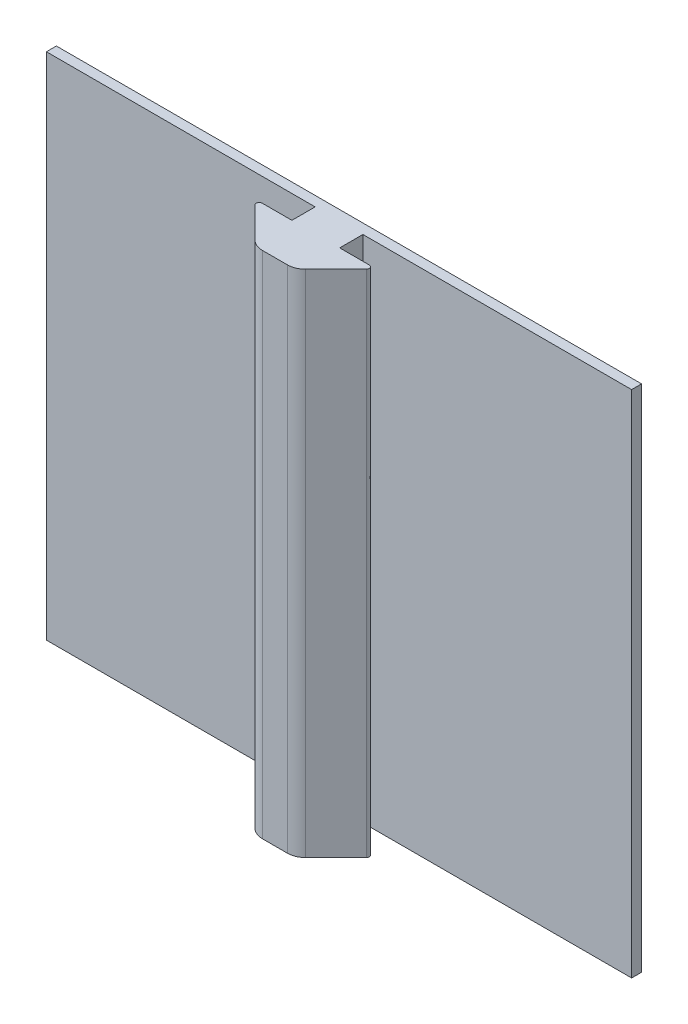
SolidWorks part; units mm, degrees
ref_plane "Front Plane" through (0, 0, 0) normal (0, 0, 1) x (1, 0, 0)
ref_plane "Top Plane" through (0, 0, 0) normal (0, 1, 0) x (1, 0, 0)
ref_plane "Right Plane" through (0, 0, 0) normal (1, 0, 0) x (0, 0, -1)
sketch "Sketch2" plane through (0, 273.2772, 0) normal (0, 1, 0) x (1, 0, 0)
  line L71 (-29.4517, 3.1399) -> (-29.4517, 3.3117)
  line L72 (-29.4517, 3.3117) -> (-63.7417, 3.3117)
  line L73 (-26.4037, -5.1151) -> (-26.4037, 8.1768) construction
  line L74 (-24.8068, -5.1151) -> (-28.0005, -5.1151) construction
  line L75 (-23.3557, 3.3117) -> (10.9343, 3.3117)
  line L76 (-23.3557, 3.1399) -> (-23.3557, 3.3117)
  line L77 (-63.7417, 3.3117) -> (-63.7417, 4.5817)
  line L78 (-29.4517, 0.3459) -> (-29.4517, 3.1399)
  line L79 (-33.2346, 0.3459) -> (-29.4517, 0.3459)
  line L80 (-29.6169, -4.1915) -> (-33.504, -0.3045)
  line L81 (-24.8068, -4.8611) -> (-28.0005, -4.8611)
  line L82 (-19.3033, -0.3045) -> (-23.1904, -4.1915)
  line L83 (-23.3557, 0.3459) -> (-19.5727, 0.3459)
  line L84 (-23.3557, 3.1399) -> (-23.3557, 0.3459)
  line L85 (-29.4517, 0.3459) -> (-29.4517, 3.1399)
  line L86 (-33.2346, 0.3459) -> (-29.4517, 0.3459)
  line L87 (-29.6169, -4.1915) -> (-33.504, -0.3045)
  line L88 (-24.8068, -4.8611) -> (-28.0005, -4.8611)
  line L89 (-19.3033, -0.3045) -> (-23.1904, -4.1915)
  line L90 (-23.3557, 0.3459) -> (-19.5727, 0.3459)
  line L91 (-23.3557, 3.1399) -> (-23.3557, 0.3459)
  line L92 (-63.7417, 4.5817) -> (10.9343, 4.5817)
  line L93 (10.9343, 4.5817) -> (10.9343, 3.3117)
  arc A44 (-33.2346, 0.3459) -> (-33.504, -0.3045) centre (-33.2346, -0.0351) ccw
  arc A45 (-29.6169, -4.1915) -> (-28.0005, -4.8611) centre (-28.0005, -2.5751) ccw
  arc A46 (-24.8068, -4.8611) -> (-23.1904, -4.1915) centre (-24.8068, -2.5751) ccw
  arc A47 (-19.3033, -0.3045) -> (-19.5727, 0.3459) centre (-19.5727, -0.0351) ccw
  arc A48 (-33.2346, 0.3459) -> (-33.504, -0.3045) centre (-33.2346, -0.0351) ccw
  arc A49 (-29.6169, -4.1915) -> (-28.0005, -4.8611) centre (-28.0005, -2.5751) ccw
  arc A50 (-24.8068, -4.8611) -> (-23.1904, -4.1915) centre (-24.8068, -2.5751) ccw
  arc A51 (-19.3033, -0.3045) -> (-19.5727, 0.3459) centre (-19.5727, -0.0351) ccw
  dimension "D2" = 1.27
  dimension "D3" = 34.29
  dimension "D1" = 0.254
extrude "Boss-Extrude1" add sketch "Sketch2" against normal blind 65.024
sketch "Sketch8" plane through (0, 0, -4.5817) normal (0, 0, -1) x (-1, 0, 0)
  circle A0 centre (7.6243, 262.7516) radius 1.524
  circle A1 centre (58.4243, 247.5116) radius 1.524
  circle A2 centre (58.4243, 219.5716) radius 1.524
  circle A3 centre (6.3543, 214.4916) radius 1.524
  dimension "D1" = 3.048
extrude "Boss-Extrude4" add sketch "Sketch8" along normal blind 7.62
sketch "Sketch9" plane through (0, 0, -4.5817) normal (0, 0, -1) x (-1, 0, 0)
  circle A2 centre (7.6243, 262.7516) radius 2.794
  circle A3 centre (7.6243, 262.7516) radius 2.794
  circle A5 centre (58.4243, 247.5116) radius 2.794
  circle A6 centre (58.4243, 247.5116) radius 2.794
  circle A8 centre (6.3543, 214.4916) radius 2.794
  circle A9 centre (6.3543, 214.4916) radius 2.794
  circle A11 centre (58.4243, 219.5716) radius 2.794
  circle A12 centre (58.4243, 219.5716) radius 2.794
  dimension "D1" = 1.27
  dimension "D2" = 1.27
  dimension "D3" = 1.27
  dimension "D4" = 1.27
extrude "Boss-Extrude5" add sketch "Sketch9" along normal blind 3.81
